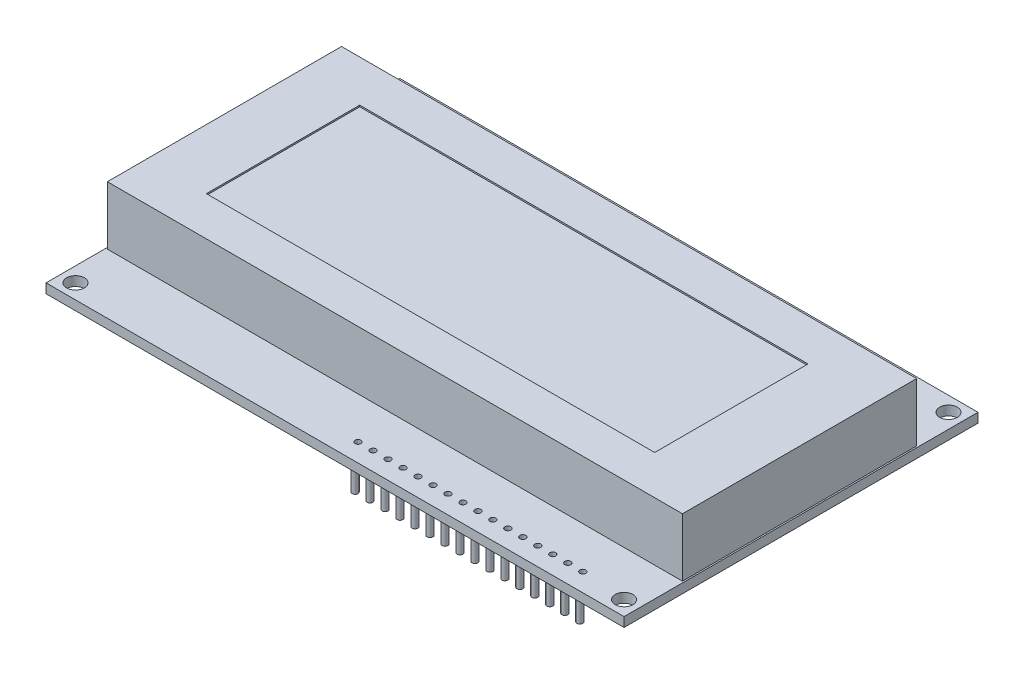
SolidWorks part; units mm, degrees
ref_plane "Front Plane" through (0, 0, 0) normal (0, 0, 1) x (1, 0, 0)
ref_plane "Top Plane" through (0, 0, 0) normal (0, 1, 0) x (1, 0, 0)
ref_plane "Right Plane" through (0, 0, 0) normal (1, 0, 0) x (0, 0, -1)
sketch "Sketch1" plane through (0, 0, 0) normal (0, 1, 0) x (1, 0, 0)
  line L1 (-72.1629, 23.3243) -> (25.8371, 23.3243)
  line L2 (-72.1629, 23.3243) -> (-72.1629, -36.6757)
  line L3 (-72.1629, -36.6757) -> (25.8371, -36.6757)
  line L4 (25.8371, 23.3243) -> (25.8371, -36.6757)
  dimension "D1" = 60
  dimension "D2" = 98
extrude "PCB board" add sketch "Sketch1" along normal blind 1.6
sketch "Sketch4" plane through (0, 1.6, 0) normal (0, 1, 0) x (1, 0, 0)
  line L4 (-72.1629, 23.3243) -> (-72.1629, -36.6757) construction
  line L6 (25.8371, 23.3243) -> (-72.1629, 23.3243) construction
  circle A0 centre (23.3371, 20.8243) radius 1.5
  circle A1 centre (-69.6629, -34.1757) radius 1.5
  circle A2 centre (-69.6629, 20.8243) radius 1.5
  circle A3 centre (23.3371, -34.1757) radius 1.5
  dimension "D3" = 2.5
  dimension "D9" = 2.5
  dimension "D2" = 2
extrude "Mounting holes" cut sketch "Sketch4" against normal blind 1.6
sketch "Sketch5" plane through (0, 1.6, 0) normal (0, 1, 0) x (1, 0, 0)
  line L0 (-72.1629, -36.6757) -> (25.8371, -36.6757) construction
  line L1 (25.8371, -36.6757) -> (25.8371, 23.3243) construction
  circle A0 centre (15.7371, -33.5757) radius 0.5
  circle A1 centre (13.1971, -33.5757) radius 0.5
  circle A2 centre (10.6571, -33.5757) radius 0.5
  circle A3 centre (8.1171, -33.5757) radius 0.5
  circle A4 centre (5.5771, -33.5757) radius 0.5
  circle A5 centre (3.0371, -33.5757) radius 0.5
  circle A6 centre (0.4971, -33.5757) radius 0.5
  circle A7 centre (-2.0429, -33.5757) radius 0.5
  circle A8 centre (-4.5829, -33.5757) radius 0.5
  circle A9 centre (-7.1229, -33.5757) radius 0.5
  circle A10 centre (-9.6629, -33.5757) radius 0.5
  circle A11 centre (-12.2029, -33.5757) radius 0.5
  circle A12 centre (-14.7429, -33.5757) radius 0.5
  circle A13 centre (-17.2829, -33.5757) radius 0.5
  circle A14 centre (-19.8229, -33.5757) radius 0.5
  circle A15 centre (-22.3629, -33.5757) radius 0.5
  dimension "D1" = 16
  dimension "D2" = 3.1
  dimension "D3" = 10.1
extrude "PCB holes" cut sketch "Sketch5" against normal blind 1.6
sketch "Sketch6" plane through (0, 0, 0) normal (0, -1, 0) x (1, 0, 0)
  circle A0 centre (-22.8629, 33.5757) radius 0.5
  circle A1 centre (-22.3629, 33.5757) radius 0.5 construction
  circle A2 centre (-20.3229, 33.5757) radius 0.5
  circle A3 centre (-17.7829, 33.5757) radius 0.5
  circle A4 centre (-15.2429, 33.5757) radius 0.5
  circle A5 centre (-12.7029, 33.5757) radius 0.5
  circle A6 centre (-10.1629, 33.5757) radius 0.5
  circle A7 centre (-7.6229, 33.5757) radius 0.5
  circle A8 centre (-5.0829, 33.5757) radius 0.5
  circle A9 centre (-2.5429, 33.5757) radius 0.5
  circle A10 centre (-0.0029, 33.5757) radius 0.5
  circle A11 centre (2.5371, 33.5757) radius 0.5
  circle A12 centre (5.0771, 33.5757) radius 0.5
  circle A13 centre (7.6171, 33.5757) radius 0.5
  circle A14 centre (10.1571, 33.5757) radius 0.5
  circle A15 centre (12.6971, 33.5757) radius 0.5
  circle A16 centre (15.2371, 33.5757) radius 0.5
  dimension "D1" = 16
extrude "Headers" add sketch "Sketch6" along normal blind 6
sketch "Sketch2" plane through (0, 1.6, 0) normal (0, 1, 0) x (1, 0, 0)
  line L0 (-72.1629, 23.3243) -> (-72.1629, -36.6757) construction
  line L1 (-71.9129, 13.1743) -> (25.5871, 13.1743)
  line L2 (-71.9129, 13.1743) -> (-71.9129, -26.5257)
  line L3 (-71.9129, -26.5257) -> (25.5871, -26.5257)
  line L4 (25.5871, 13.1743) -> (25.5871, -26.5257)
  line L5 (-72.1629, -36.6757) -> (25.8371, -36.6757) construction
  point P4 (-23.1629, 13.1743)
  point P7 (-71.9129, -6.6757)
  dimension "D1" = 97.5
  dimension "D2" = 39.7
  dimension "D3" = 49
  dimension "D4" = 30
extrude "Black LCD frame" add sketch "Sketch2" along normal blind 9.9
sketch "Sketch7" plane through (-71.9129, 0, 0) normal (-1, 0, 0) x (0, 0, 1)
  line L0 (-13.1743, 1.6) -> (26.5257, 1.6) construction
  line L1 (11, 4.6) -> (0, 4.6)
  line L2 (11, 4.6) -> (11, 1.6)
  line L3 (11, 1.6) -> (0, 1.6)
  line L4 (0, 4.6) -> (0, 1.6)
  dimension "D1" = 11
  dimension "D2" = 3
extrude "White part that sticks out" add sketch "Sketch7" along normal blind 2.17
sketch "Sketch3" plane through (0, 11.5, 0) normal (0, 1, 0) x (1, 0, 0)
  line L1 (-61.7665, 6.1117) -> (14.2335, 6.1117)
  line L2 (-61.7665, 6.1117) -> (-61.7665, -19.8883)
  line L3 (-61.7665, -19.8883) -> (14.2335, -19.8883)
  line L4 (14.2335, 6.1117) -> (14.2335, -19.8883)
  dimension "D1" = 26
  dimension "D2" = 76
extrude "LCD screen" cut sketch "Sketch3" against normal blind 0.254
sketch "Sketch8" plane through (0, 0, 0) normal (0, -1, 0) x (1, 0, 0)
  line L1 (-66.2179, 30.7989) -> (-65.5253, 30.7989)
  line L2 (-66.2179, 30.7989) -> (-66.2179, 27.1142)
  line L3 (-66.2179, 27.1142) -> (-65.5253, 27.1142)
  line L4 (-65.5253, 30.7989) -> (-65.5253, 27.1142)
  line L5 (-65.8716, -13.7174) -> (-65.5253, -13.7174)
  line L6 (-65.8716, -13.7174) -> (-65.8716, -18.1155)
  line L7 (-65.8716, -18.1155) -> (-65.5253, -18.1155)
  line L8 (-65.5253, -13.7174) -> (-65.5253, -18.1155)
  line L9 (-26.9357, -13.7174) -> (-25.7637, -13.7174)
  line L10 (-26.9357, -13.7174) -> (-26.9357, -18.1155)
  line L11 (-26.9357, -18.1155) -> (-25.7637, -18.1155)
  line L12 (-25.7637, -13.7174) -> (-25.7637, -18.1155)
  line L13 (16.5491, -13.7174) -> (17.559, -13.7174)
  line L14 (16.5491, -13.7174) -> (16.5491, -18.1155)
  line L15 (16.5491, -18.1155) -> (17.559, -18.1155)
  line L16 (17.559, -13.7174) -> (17.559, -18.1155)
  line L17 (17.559, 27.1142) -> (18.6169, 27.1142)
  line L18 (17.559, 27.1142) -> (17.559, 30.7989)
  line L19 (17.559, 30.7989) -> (18.6169, 30.7989)
  line L20 (18.6169, 27.1142) -> (18.6169, 30.7989)
  line L21 (-26.9357, 30.7989) -> (-26.3497, 30.7989)
  line L22 (-26.9357, 30.7989) -> (-26.9357, 27.1142)
  line L23 (-26.9357, 27.1142) -> (-26.3497, 27.1142)
  line L24 (-26.3497, 30.7989) -> (-26.3497, 27.1142)
extrude "Boss-Extrude1" add sketch "Sketch8" along normal blind 2.5
equation "\"D3@Sketch2\" = \"D2@Sketch1\"/2"
equation "\"D4@Sketch2\" = \"D1@Sketch1\"/2"
